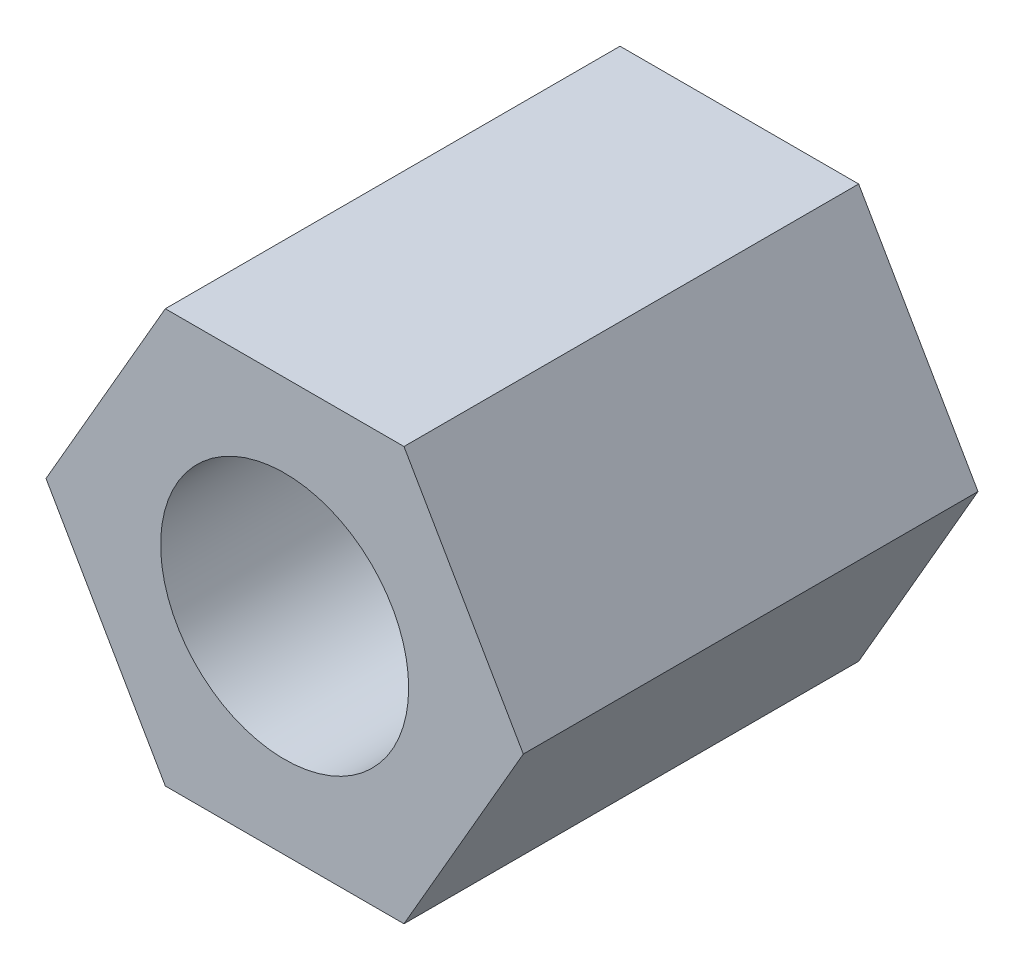
SolidWorks part; units mm, degrees
material "1.0301 (C10)"
ref_plane "Piano frontale" through (0, 0, 0) normal (0, 0, 1) x (1, 0, 0)
ref_plane "Piano superiore" through (0, 0, 0) normal (0, 1, 0) x (1, 0, 0)
ref_plane "Piano destro" through (0, 0, 0) normal (1, 0, 0) x (0, 0, -1)
sketch "Schizzo1" plane through (0, 0, 0) normal (0, 0, 1) x (1, 0, 0)
  line L1 (1.4434, 2.5) -> (-1.4434, 2.5)
  line L2 (-1.4434, 2.5) -> (-2.8868, 0)
  line L3 (-2.8868, 0) -> (-1.4434, -2.5)
  line L4 (-1.4434, -2.5) -> (1.4434, -2.5)
  line L5 (1.4434, -2.5) -> (2.8868, 0)
  line L6 (2.8868, 0) -> (1.4434, 2.5)
  circle A0 centre (0, 0) radius 2.5 construction
  dimension "D1" = 5
extrude "Estrusione-Estrusione1" add sketch "Schizzo1" along normal blind 5.5
sketch "Schizzo2" plane through (0, 0, 5.5) normal (0, 0, 1) x (1, 0, 0)
  circle A0 centre (0, 0) radius 1.5
  dimension "D1" = 3
extrude "Taglio-Estrusione1" cut sketch "Schizzo2" against normal blind 15
